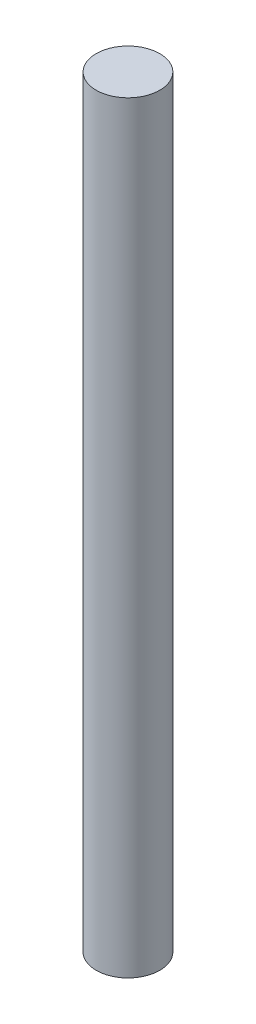
SolidWorks part; units mm, degrees
material "AISI 316 Annealed Stainless Steel Bar (SS)"
ref_plane "Front Plane" through (0, 0, 0) normal (0, 0, 1) x (1, 0, 0)
ref_plane "Top Plane" through (0, 0, 0) normal (0, 1, 0) x (1, 0, 0)
ref_plane "Right Plane" through (0, 0, 0) normal (1, 0, 0) x (0, 0, -1)
sketch "Sketch1" plane through (0, 0, 0) normal (0, 0, 1) x (1, 0, 0)
  line L0 (0, 0) -> (-1.5875, 0)
  line L1 (-1.5875, 0) -> (-1.5875, 38.1)
  line L2 (-1.5875, 38.1) -> (0, 38.1)
  line L3 (0, 38.1) -> (0, 0)
  dimension "D1" = 1.5875
  dimension "D2" = 38.1
revolve "Revolve1" add sketch "Sketch1" angle 360 about L3
